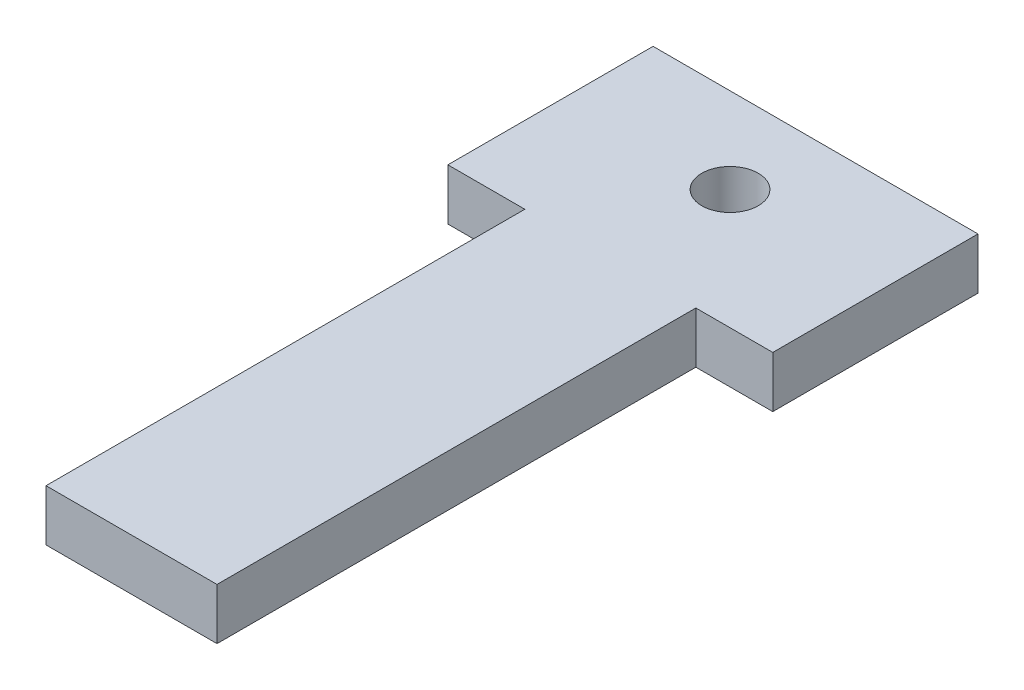
SolidWorks part; units mm, degrees
ref_plane "Front Plane" through (0, 0, 0) normal (0, 0, 1) x (1, 0, 0)
ref_plane "Top Plane" through (0, 0, 0) normal (0, 1, 0) x (1, 0, 0)
ref_plane "Right Plane" through (0, 0, 0) normal (1, 0, 0) x (0, 0, -1)
sketch "Sketch1" plane through (0, 0, 0) normal (0, 1, 0) x (1, 0, 0)
  line L0 (-5, -35) -> (5, -35)
  line L1 (5, -35) -> (5, 5)
  line L4 (5, 5) -> (-5, 5)
  line L5 (-5, 5) -> (-5, -35)
  line L7 (9.5, -7) -> (5, -7)
  line L8 (9.5, -7) -> (9.5, 5)
  line L9 (9.5, 5) -> (5, 5)
  line L10 (5, -7) -> (5, 5)
  line L11 (9.5, -7) -> (5, 5) construction
  line L12 (9.5, 5) -> (5, -7) construction
  line L13 (-9.5, -7) -> (-5, -7)
  line L14 (-9.5, -7) -> (-9.5, 5)
  line L15 (-9.5, 5) -> (-5, 5)
  line L16 (-5, -7) -> (-5, 5)
  line L17 (-9.5, -7) -> (-5, 5) construction
  line L18 (-9.5, 5) -> (-5, -7) construction
  circle A0 centre (0, 0) radius 1.65
  point P4 (-7.25, -1)
  point P5 (7.25, -1)
  point P10 (0, -35)
  dimension "D3" = 3.3
  dimension "D1" = 10
  dimension "D2" = 40
  dimension "D4" = 5
  dimension "D5" = 4.5
  dimension "D6" = 12
extrude "Boss-Extrude1" add sketch "Sketch1" along normal blind 3 contours L4 L5 L0 L1 A0 | L15 L14 L13 L5 | L8 L9 L1 L7
